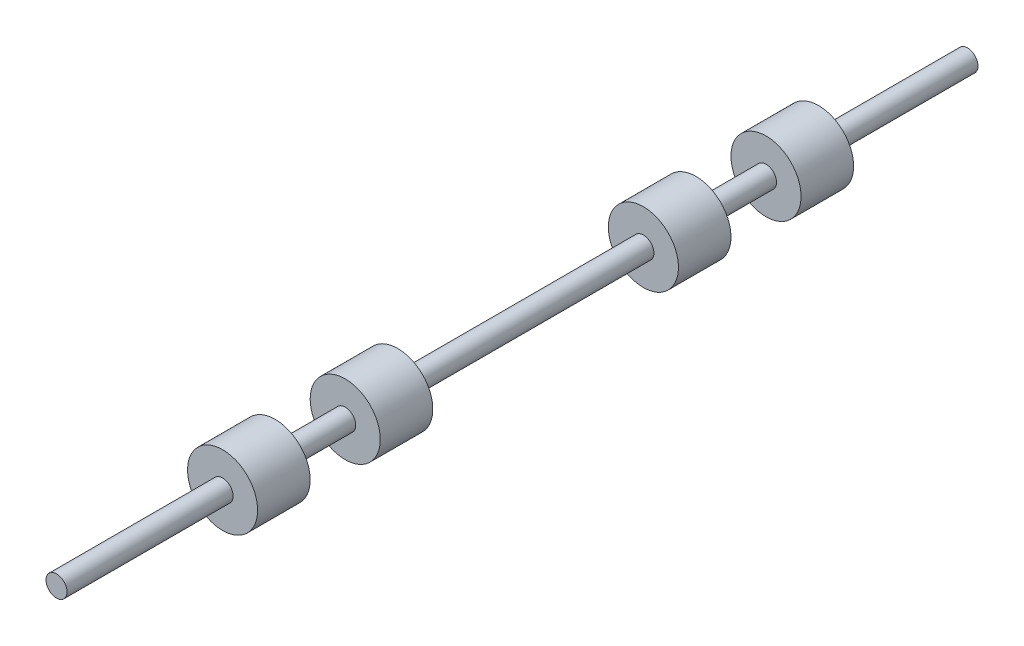
SolidWorks part; units mm, degrees
ref_plane "Front Plane" through (0, 0, 0) normal (0, 0, 1) x (1, 0, 0)
ref_plane "Top Plane" through (0, 0, 0) normal (0, 1, 0) x (1, 0, 0)
ref_plane "Right Plane" through (0, 0, 0) normal (1, 0, 0) x (0, 0, -1)
sketch "Sketch1" plane through (0, 0, 0) normal (0, 0, 1) x (1, 0, 0)
  circle A0 centre (0, 0) radius 0.3
  dimension "D1" = 0.6
extrude "Boss-Extrude1" add sketch "Sketch1" along normal blind 26
sketch "Sketch3" plane through (0, 0, 0) normal (0, 1, 0) x (1, 0, 0)
  line L0 (0, 0) -> (0, -26) construction
  line L1 (-0.3, -26) -> (0.3, -26) construction
  line L2 (0, -6.75) -> (3.1642, -6.75) construction
  line L3 (0, -4.25) -> (1, -4.25)
  line L4 (0, -4.25) -> (0, -5.75)
  line L5 (0, -5.75) -> (1, -5.75)
  line L6 (1, -4.25) -> (1, -5.75)
  line L7 (0, -7.75) -> (1, -7.75)
  line L8 (0, -7.75) -> (0, -9.25)
  line L9 (0, -9.25) -> (1, -9.25)
  line L10 (1, -7.75) -> (1, -9.25)
  line L11 (0, -18.76) -> (9.3693, -18.76) construction
  line L12 (0, -16.26) -> (1, -16.26)
  line L13 (0, -16.26) -> (0, -17.76)
  line L14 (0, -17.76) -> (1, -17.76)
  line L15 (1, -16.26) -> (1, -17.76)
  line L16 (0, -19.76) -> (1, -19.76)
  line L17 (0, -19.76) -> (0, -21.26)
  line L18 (0, -21.26) -> (1, -21.26)
  line L19 (1, -19.76) -> (1, -21.26)
  dimension "D1" = 1.5
  dimension "D2" = 1.5
  dimension "D3" = 1
  dimension "D4" = 1
  dimension "D5" = 2
  dimension "D6" = 1.5
  dimension "D7" = 1.5
  dimension "D8" = 1
  dimension "D9" = 1
  dimension "D10" = 2
  dimension "D11" = 12.01
  dimension "D12" = 7.24
revolve "Revolve1" add sketch "Sketch3" angle 360 about L0
